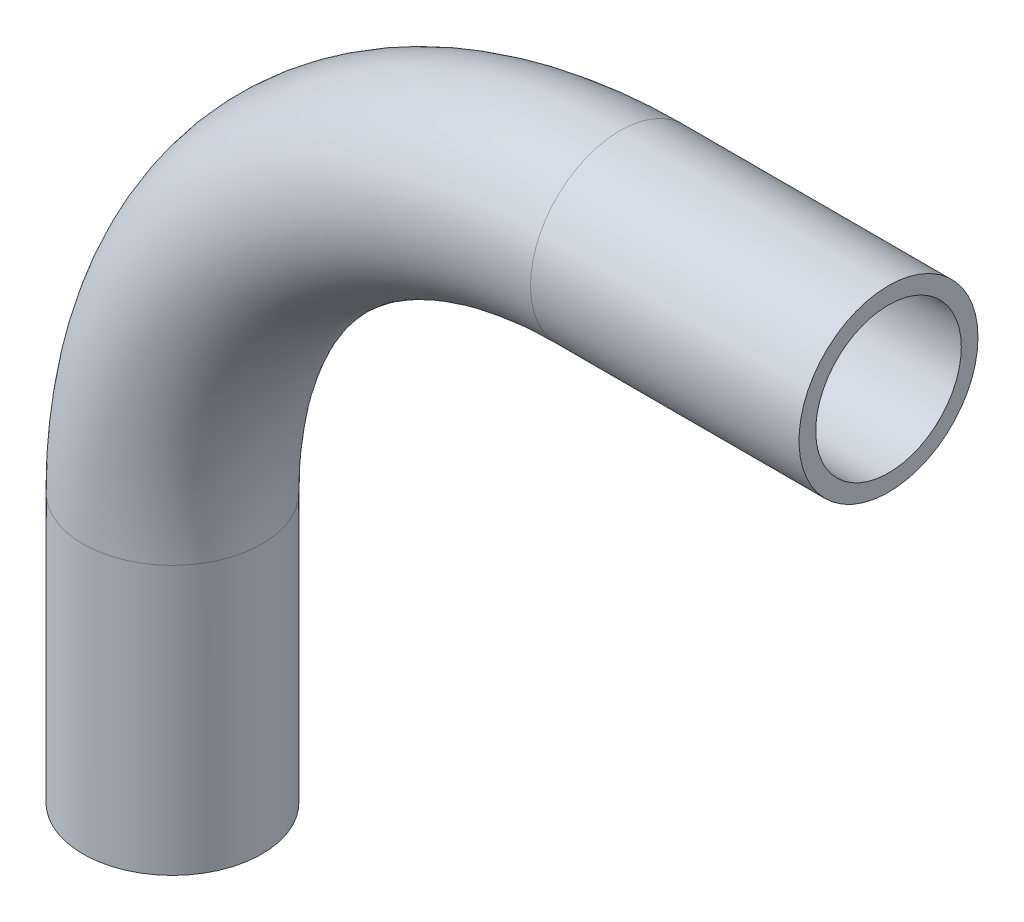
SolidWorks part; units mm, degrees
material "6061-T6 (SS)"
ref_plane "Front Plane" through (0, 0, 0) normal (0, 0, 1) x (1, 0, 0)
ref_plane "Top Plane" through (0, 0, 0) normal (0, 1, 0) x (1, 0, 0)
ref_plane "Right Plane" through (0, 0, 0) normal (1, 0, 0) x (0, 0, -1)
sketch "Sketch1" plane through (0, 0, 0) normal (0, 0, 1) x (1, 0, 0)
  line L0 (0, -23.8125) -> (0, -38.1)
  line L1 (23.8125, 0) -> (38.1, 0)
  arc A0 (0, -23.8125) -> (23.8125, 0) centre (23.8125, -23.8125) cw
  point P6 (0, 0)
  dimension "D3" = 23.8125
  dimension "D1" = 38.1
  dimension "D2" = 38.1
  dimension "D4" = 90
ref_plane "Plane1" through (38.1, 0, 0) normal (1, 0, 0) x (0, 0, -1)
sketch "Sketch2" plane through (38.1, 0, 0) normal (1, 0, 0) x (0, 0, -1)
  circle A0 centre (0, 0) radius 4.7625
  circle A1 centre (0, 0) radius 3.8735
  dimension "D1" = 9.525
  dimension "D2" = 7.747
sweep "Sweep1" add profiles "Sketch2" path "Sketch1"
